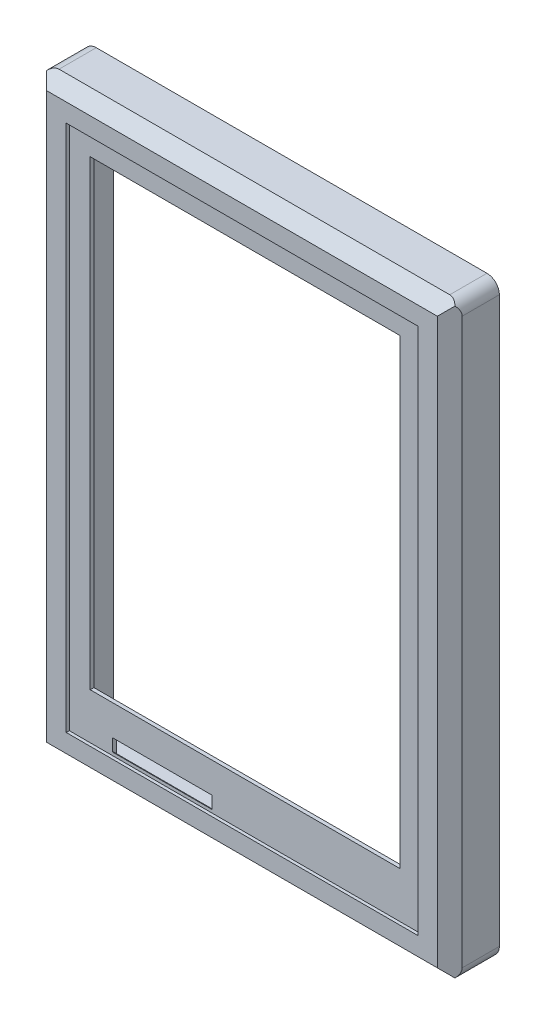
SolidWorks part; units mm, degrees
material "PUR"
ref_plane "Front" through (0, 0, 0) normal (0, 0, 1) x (1, 0, 0)
ref_plane "Top" through (0, 0, 0) normal (0, 1, 0) x (1, 0, 0)
ref_plane "Right" through (0, 0, 0) normal (1, 0, 0) x (0, 0, -1)
sketch "Skizze1" plane through (0, 0, 0) normal (0, 0, 1) x (1, 0, 0)
  line L1 (0, 0) -> (67, 0)
  line L2 (0, 0) -> (0, 95)
  line L3 (0, 95) -> (67, 95)
  line L4 (67, 0) -> (67, 95)
extrude "Aufsatz-Linear austragen1" add sketch "Skizze1" along normal blind 8
sketch "Skizze2" plane through (0, 0, 8) normal (0, 0, 1) x (1, 0, 0)
  line L0 (67, 95) -> (0, 95) construction
  line L1 (5.15, 90.05) -> (61.85, 90.05)
  line L2 (5.15, 90.05) -> (5.15, 4.95)
  line L3 (5.15, 4.95) -> (61.85, 4.95)
  line L4 (61.85, 90.05) -> (61.85, 4.95)
  line L5 (0, 95) -> (0, 0) construction
extrude "Schnitt-Linear austragen1" cut sketch "Skizze2" against normal blind 0.5
sketch "Skizze3" plane through (0, 0, 7.5) normal (0, 0, 1) x (1, 0, 0)
  line L0 (61.85, 90.05) -> (5.15, 90.05) construction
  line L1 (8.52, 86.79) -> (58.48, 86.79)
  line L2 (8.52, 86.79) -> (8.52, 12.35)
  line L3 (8.52, 12.35) -> (58.48, 12.35)
  line L4 (58.48, 86.79) -> (58.48, 12.35)
  line L5 (67, 0) -> (67, 95) construction
extrude "Schnitt-Linear austragen2" cut sketch "Skizze3" against normal up to next and the other way up to surface
sketch "Skizze4" plane through (0, 0, 7.5) normal (0, 0, 1) x (1, 0, 0)
  line L0 (5.15, 90.05) -> (5.15, 4.95) construction
  line L1 (12.15, 7.45) -> (28.15, 7.45)
  line L2 (12.15, 7.45) -> (12.15, 5.45)
  line L3 (12.15, 5.45) -> (28.15, 5.45)
  line L4 (28.15, 7.45) -> (28.15, 5.45)
  line L6 (5.15, 4.95) -> (61.85, 4.95) construction
  dimension "D1" = 7
  dimension "D2" = 16
  dimension "D3" = 2
  dimension "D4" = 0.5
extrude "Schnitt-Linear austragen3" cut sketch "Skizze4" against normal up to next
sketch "Skizze5" plane through (0, 0, 0) normal (0, 0, -1) x (-1, 0, 0)
  line L0 (-67, 0) -> (-67, 95) construction
  line L1 (-61.9, 90.15) -> (-5.1, 90.15)
  line L2 (-61.9, 90.15) -> (-61.9, 4.85)
  line L3 (-61.9, 4.85) -> (-5.1, 4.85)
  line L4 (-5.1, 90.15) -> (-5.1, 4.85)
  line L5 (-67, 95) -> (0, 95) construction
extrude "Schnitt-Linear austragen4" cut sketch "Skizze5" against normal offset from surface (6.9 mm away) 0.6 up to face at (20.15, 6.45, 7.5)
chamfer "Fase1" distance 2 angle 45 4 edges at (0, 47.5, 8) (33.5, 0, 8) (67, 47.5, 8) (33.5, 95, 8)
chamfer "Fase2" distance 0.5 angle 45 1 edges at (20.15, 5.45, 6.9)
sketch "Skizze8" plane through (0, 90.15, 0) normal (0, -1, 0) x (1, 0, 0)
  line L1 (61.9, 6.9) -> (5.1, 6.9)
  line L2 (61.9, 6.9) -> (61.9, 3.9)
  line L3 (61.9, 3.9) -> (5.1, 3.9)
  line L4 (5.1, 6.9) -> (5.1, 3.9)
  line L5 (5.1, 6.9) -> (5.1, 0) construction
  dimension "D1" = 3
extrude "Schnitt-Linear austragen5" cut sketch "Skizze8" against normal blind 2
sketch "Skizze10" plane through (0, 90.15, 0) normal (0, -1, 0) x (1, 0, 0)
  line L0 (5.1, 3.9) -> (5.1, 0) construction
  line L1 (61.9, 3.9) -> (5.1, 3.9)
  line L2 (61.9, 3.9) -> (61.9, 2.4)
  line L3 (61.9, 2.4) -> (5.1, 2.4)
  line L4 (5.1, 3.9) -> (5.1, 2.4)
  dimension "D1" = 1.5
extrude "Aufsatz-Linear austragen2" add sketch "Skizze10" along normal up to surface (85.3 mm away) up to face at (33.5, 4.85, 3.45)
sketch "Skizze12" plane through (0, 0, 2.4) normal (0, 0, -1) x (-1, 0, 0)
  line L0 (-61.9, 4.85) -> (-61.9, 90.15) construction
  line L1 (-61.9, 88.65) -> (-5.1, 88.65)
  line L2 (-61.9, 88.65) -> (-61.9, 6.35)
  line L3 (-61.9, 6.35) -> (-5.1, 6.35)
  line L4 (-5.1, 88.65) -> (-5.1, 6.35)
  line L5 (-5.1, 4.85) -> (-5.1, 90.15) construction
  line L6 (-5.1, 90.15) -> (-61.9, 90.15) construction
  line L7 (-5.1, 4.85) -> (-61.9, 4.85) construction
  dimension "D1" = 1.5
  dimension "D2" = 1.5
extrude "Schnitt-Linear austragen6" cut sketch "Skizze12" against normal up to next
fillet "Verrundung2" radius 2 4 edges at (0, 0, 3) (67, 0, 3) (0, 95, 3) (67, 95, 3)
sketch "Skizze14" plane through (0, 0, 0) normal (0, 0, -1) x (-1, 0, 0)
  line L4 (-65, 0) -> (-2, 0)
  line L5 (0, 2) -> (0, 93)
  line L6 (-2, 95) -> (-65, 95)
  line L7 (-67, 93) -> (-67, 2)
  line L8 (-65, 0) -> (-2, 0)
  line L9 (0, 2) -> (0, 93)
  line L10 (-2, 95) -> (-65, 95)
  line L11 (-67, 93) -> (-67, 2)
  line L13 (-64, 94) -> (-3, 94)
  line L14 (-66, 92) -> (-66, 3)
  line L15 (-64, 1) -> (-3, 1)
  line L16 (-1, 92) -> (-1, 3)
  line L17 (-62.8, 2.2) -> (-4.2, 2.2)
  line L18 (-64.8, 4.2) -> (-64.8, 90.8)
  line L19 (-62.8, 92.8) -> (-4.2, 92.8)
  line L20 (-2.2, 4.2) -> (-2.2, 90.8)
  arc A4 (-2, 0) -> (0, 2) centre (-2, 2) ccw
  arc A5 (0, 93) -> (-2, 95) centre (-2, 93) ccw
  arc A6 (-65, 95) -> (-67, 93) centre (-65, 93) ccw
  arc A7 (-67, 2) -> (-65, 0) centre (-65, 2) ccw
  arc A8 (-2, 0) -> (0, 2) centre (-2, 2) ccw
  arc A9 (0, 93) -> (-2, 95) centre (-2, 93) ccw
  arc A10 (-65, 95) -> (-67, 93) centre (-65, 93) ccw
  arc A11 (-67, 2) -> (-65, 0) centre (-65, 2) ccw
  arc A12 (-66, 3) -> (-64, 1) centre (-64, 3) ccw
  arc A13 (-3, 1) -> (-1, 3) centre (-3, 3) ccw
  arc A14 (-3, 94) -> (-1, 92) centre (-3, 92) cw
  arc A15 (-64, 94) -> (-66, 92) centre (-64, 92) ccw
  arc A16 (-2.2, 4.2) -> (-4.2, 2.2) centre (-4.2, 4.2) cw
  arc A17 (-2.2, 90.8) -> (-4.2, 92.8) centre (-4.2, 90.8) ccw
  arc A18 (-62.8, 92.8) -> (-64.8, 90.8) centre (-62.8, 90.8) ccw
  arc A19 (-64.8, 4.2) -> (-62.8, 2.2) centre (-62.8, 4.2) ccw
  dimension "D6" = 2
  dimension "D11" = 2
  dimension "D2" = 1
  dimension "D3" = 1
  dimension "D4" = 1
  dimension "D5" = 1
  dimension "D7" = 1.2
  dimension "D8" = 1.2
  dimension "D9" = 1.2
  dimension "D10" = 1.2
  dimension "D1" = 0
chamfer "Fase3" distance 3 angle 15 1 edges at (33.5, 88.65, 3.9)
sketch "Skizze17" plane through (0, 0, 6.9) normal (0, 0, -1) x (-1, 0, 0)
  line L1 (-59.08, 87.39) -> (-7.92, 87.39)
  line L2 (-59.08, 87.39) -> (-59.08, 11.75)
  line L3 (-59.08, 11.75) -> (-7.92, 11.75)
  line L4 (-7.92, 87.39) -> (-7.92, 11.75)
  line L5 (-58.48, 86.79) -> (-8.52, 86.79)
  line L6 (-58.48, 86.79) -> (-58.48, 12.35)
  line L7 (-58.48, 12.35) -> (-8.52, 12.35)
  line L8 (-8.52, 86.79) -> (-8.52, 12.35)
  dimension "D1" = 0.6
  dimension "D2" = 0.6
  dimension "D3" = 0.6
  dimension "D4" = 0.6
extrude "Aufsatz-Linear austragen6" [suppressed] add sketch "Skizze17" along normal up to surface (7.1 mm away)
extrude "Schnitt-Linear austragen9" cut sketch "Skizze14" against normal blind 3 contours L13 A15 L14 A12 L15 A13 L16 A14 A19 L18 A18 L19 A17 L20 A16 L17
chamfer "Fase8" distance 0.3 angle 45 12 edges at (64.2142, 92.2142, 0) (33.5, 92.8, 0) (2.7858, 92.2142, 0) (2.2, 47.5, 0) (2.7858, 2.7858, 0) (33.5, 2.2, 0) (64.2142, 2.7858, 0) (64.8, 47.5, 0) (5.1, 47.5, 0) (33.5, 90.15, 0) (61.9, 47.5, 0) (33.5, 4.85, 0)
ref_plane "Ebene2" through (33.5, 0, 0) normal (-1, 0, 0) x (0, 0, 1)
sketch "Skizze18" plane through (5.1, 0, 0) normal (1, 0, 0) x (0, 0, -1)
  line L0 (0, 95) -> (-6, 95) construction
  line L1 (-4, 83) -> (-5.65, 83)
  line L2 (-4, 83) -> (-4, 78.6)
  line L3 (-4, 78.6) -> (-5.65, 78.6)
  line L4 (-5.65, 83) -> (-5.65, 78.6)
  line L6 (0, 90.45) -> (0, 4.55) construction
  dimension "D1" = 12
  dimension "D2" = 1.65
  dimension "D3" = 4.4
  dimension "D4" = 4
extrude "Schnitt-Linear austragen10" cut sketch "Skizze18" against normal offset from surface (4.1 mm away) 1 up to face at (0, 47.5, 3)
mirror "Spiegeln6" about plane through (33.5, 0, 0) normal (-1, 0, 0) of "Schnitt-Linear austragen10"
sketch "Skizze20" plane through (0, 0, 5.65) normal (0, 0, -1) x (-1, 0, 0)
  line L0 (-1, 78.6) -> (-1, 83) construction
  line L8 (-1, 80.8) -> (-5.1, 80.8) construction
  line L9 (-5.1, 83) -> (-5.1, 78.6) construction
  line L10 (-1, 78.6) -> (-5.1, 78.6) construction
  line L11 (-1, 83) -> (-5.1, 83) construction
  circle A0 centre (-3, 80.8) radius 1.75
  dimension "D2" = 3.5
  dimension "D1" = 2
extrude "Aufsatz-Linear austragen7" add sketch "Skizze20" along normal up to surface (4 mm away) from surface at 1.65 up to face at (33.5, 47.5, 0) starting at face at (3.05, 80.8, 4)
sketch "Skizze21" plane through (0, 0, 5.65) normal (0, 0, -1) x (-1, 0, 0)
  circle A0 centre (-3, 80.8) radius 1.05
  dimension "D1" = 2.1
extrude "Schnitt-Linear austragen12" cut sketch "Skizze21" along normal up to surface (5.65 mm away) and the other way blind 1 up to face at (27.175, 54.16, 0)
mirror "Spiegeln1" about plane through (33.5, 0, 0) normal (-1, 0, 0) of "Schnitt-Linear austragen12", "Aufsatz-Linear austragen7"
sketch "Skizze22" plane through (0, 0, 0) normal (0, 0, -1) x (-1, 0, 0)
  line L0 (-33.5, 99.9812) -> (-33.5, -9.9956) construction
  line L1 (-67, 2) -> (-67, 93) construction
  line L2 (0, 93) -> (0, 2) construction
sketch3d "3D-Skizze1" plane through (0, 0, 0) normal (0, 0, 1) x (1, 0, 0)
  dimension "D1" = 28.4
pattern_linear "Lineares Muster1" count 2 spacing 68.8 along (0, -1, 0) of "Schnitt-Linear austragen10", "Aufsatz-Linear austragen7", "Schnitt-Linear austragen12", "Spiegeln1", "Spiegeln6"
equation "\"D3@Skizze2\"=(\"hoehe@Skizze1\"-\"D2@Skizze2\")/2"
equation "\"D4@Skizze2\"=(\"breite@Skizze1\"-\"D1@Skizze2\")/2"
equation "\"D4@Skizze3\"=(\"breite@Skizze1\"-\"D3@Skizze3\")/2"
equation "\"D2@Skizze5\"=(\"breite@Skizze1\"-\"D1@Skizze5\")/2"
equation "\"D4@Skizze5\"=(\"hoehe@Skizze1\"-\"D3@Skizze5\")/2"
